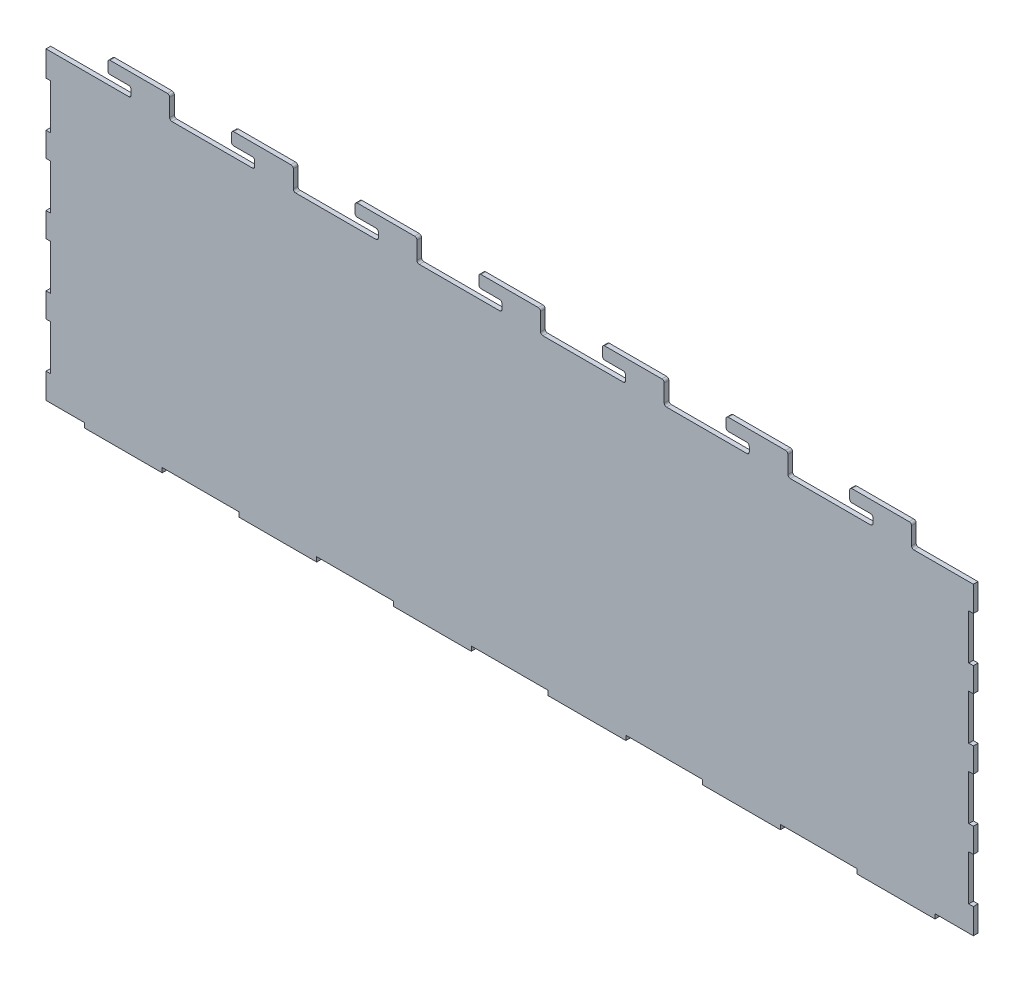
SolidWorks part; units mm, degrees
ref_plane "Alzado" through (0, 0, 0) normal (0, 0, 1) x (1, 0, 0)
ref_plane "Planta" through (0, 0, 0) normal (0, 1, 0) x (1, 0, 0)
ref_plane "Vista lateral" through (0, 0, 0) normal (1, 0, 0) x (0, 0, -1)
sketch "Croquis1" plane through (0, 0, 0) normal (0, 0, 1) x (1, 0, 0)
  line L1 (-300, 100) -> (300, 100)
  line L2 (-300, 100) -> (-300, -100)
  line L3 (-300, -100) -> (300, -100)
  line L4 (300, 100) -> (300, -100)
  line L5 (-300, 100) -> (300, -100) construction
  line L6 (-300, -100) -> (300, 100) construction
  point P0 (0, 0)
  dimension "D1" = 600
  dimension "D2" = 200
extrude "Saliente-Extruir1" add sketch "Croquis1" along normal blind 3
sketch "Croquis2" plane through (0, 0, 0) normal (0, 0, -1) x (-1, 0, 0)
  line L4 (-300, 100) -> (-300, -100)
  line L5 (-300, -100) -> (300, -100)
  line L6 (300, -100) -> (300, 100)
  line L7 (300, 100) -> (-300, 100)
  line L9 (-300, -100) -> (300, -100)
  line L11 (300, 100) -> (-300, 100)
  line L68 (224.85, -100) -> (275.15, -100)
  line L69 (275.15, -100) -> (275.15, -97)
  line L70 (275.15, -97) -> (300, -97)
  line L71 (300, -97) -> (300, -81)
  line L72 (300, -81) -> (297, -81)
  line L73 (297, -81) -> (297, -51)
  line L74 (297, -51) -> (300, -51)
  line L75 (300, -51) -> (300, -36)
  line L76 (300, -36) -> (297, -36)
  line L77 (297, -36) -> (297, -6)
  line L78 (297, -6) -> (300, -6)
  line L79 (300, -6) -> (300, 9)
  line L80 (300, 9) -> (297, 9)
  line L81 (297, 9) -> (297, 39)
  line L82 (297, 39) -> (300, 39)
  line L83 (300, 39) -> (300, 54)
  line L84 (300, 54) -> (297, 54)
  line L85 (297, 54) -> (297, 84)
  line L86 (297, 84) -> (300, 84)
  line L87 (300, 84) -> (300, 100)
  line L88 (300, 100) -> (-300, 100)
  line L89 (-300, 100) -> (-300, 84)
  line L90 (-300, 84) -> (-297, 84)
  line L91 (-297, 84) -> (-297, 54)
  line L92 (-297, 54) -> (-300, 54)
  line L93 (-300, 54) -> (-300, 39)
  line L94 (-300, 39) -> (-297, 39)
  line L95 (-297, 39) -> (-297, 9)
  line L96 (-297, 9) -> (-300, 9)
  line L97 (-300, 9) -> (-300, -6)
  line L98 (-300, -6) -> (-297, -6)
  line L99 (-297, -6) -> (-297, -36)
  line L100 (-297, -36) -> (-300, -36)
  line L101 (-300, -36) -> (-300, -51)
  line L102 (-300, -51) -> (-297, -51)
  line L103 (-297, -51) -> (-297, -81)
  line L104 (-297, -81) -> (-300, -81)
  line L105 (-300, -81) -> (-300, -97)
  line L106 (-300, -97) -> (-275.15, -97)
  line L107 (-275.15, -97) -> (-275.15, -100)
  line L108 (-275.15, -100) -> (-224.85, -100)
  line L109 (-224.85, -100) -> (-224.85, -97)
  line L110 (-224.85, -97) -> (-175.15, -97)
  line L111 (-175.15, -97) -> (-175.15, -100)
  line L112 (-175.15, -100) -> (-124.85, -100)
  line L113 (-124.85, -100) -> (-124.85, -97)
  line L114 (-124.85, -97) -> (-75.15, -97)
  line L115 (-75.15, -97) -> (-75.15, -100)
  line L116 (-75.15, -100) -> (-24.85, -100)
  line L117 (-24.85, -100) -> (-24.85, -97)
  line L118 (-24.85, -97) -> (24.85, -97)
  line L119 (24.85, -97) -> (24.85, -100)
  line L120 (24.85, -100) -> (75.15, -100)
  line L121 (75.15, -100) -> (75.15, -97)
  line L122 (75.15, -97) -> (124.85, -97)
  line L123 (124.85, -97) -> (124.85, -100)
  line L124 (124.85, -100) -> (175.15, -100)
  line L125 (175.15, -100) -> (175.15, -97)
  line L126 (175.15, -97) -> (224.85, -97)
  line L127 (224.85, -97) -> (224.85, -100)
  line L128 (224.85, -100) -> (275.15, -100)
  line L129 (275.15, -100) -> (275.15, -97)
  line L130 (275.15, -97) -> (300, -97)
  line L148 (300, 100) -> (-300, 100)
  line L166 (-300, -97) -> (-275.15, -97)
  line L167 (-275.15, -97) -> (-275.15, -100)
  line L168 (-275.15, -100) -> (-224.85, -100)
  line L169 (-224.85, -100) -> (-224.85, -97)
  line L170 (-224.85, -97) -> (-175.15, -97)
  line L171 (-175.15, -97) -> (-175.15, -100)
  line L172 (-175.15, -100) -> (-124.85, -100)
  line L173 (-124.85, -100) -> (-124.85, -97)
  line L174 (-124.85, -97) -> (-75.15, -97)
  line L175 (-75.15, -97) -> (-75.15, -100)
  line L176 (-75.15, -100) -> (-24.85, -100)
  line L177 (-24.85, -100) -> (-24.85, -97)
  line L178 (-24.85, -97) -> (24.85, -97)
  line L179 (24.85, -97) -> (24.85, -100)
  line L180 (24.85, -100) -> (75.15, -100)
  line L181 (75.15, -100) -> (75.15, -97)
  line L182 (75.15, -97) -> (124.85, -97)
  line L183 (124.85, -97) -> (124.85, -100)
  line L184 (124.85, -100) -> (175.15, -100)
  line L185 (175.15, -100) -> (175.15, -97)
  line L186 (175.15, -97) -> (224.85, -97)
  line L187 (224.85, -97) -> (224.85, -100)
  line L548 (-300, -97) -> (-300, 100)
  line L549 (300, -100) -> (300, 100)
  line L731 (-297, -51.4) -> (-300, -51.4)
  line L732 (-297, -51.4) -> (-297, -80.6)
  line L733 (-297, -80.6) -> (-300, -80.6)
  line L734 (-300, -51.4) -> (-300, -80.6)
  line L1814 (-297, -6.4) -> (-297, -35.6)
  line L1815 (-297, -6.4) -> (-300, -6.4)
  line L1816 (-300, -6.4) -> (-300, -35.6)
  line L1817 (-297, -35.6) -> (-300, -35.6)
  line L1818 (-297, 38.6) -> (-297, 9.4)
  line L1819 (-297, 38.6) -> (-300, 38.6)
  line L1820 (-300, 38.6) -> (-300, 9.4)
  line L1821 (-297, 9.4) -> (-300, 9.4)
  line L1822 (-297, 83.6) -> (-297, 54.4)
  line L1823 (-297, 83.6) -> (-300, 83.6)
  line L1824 (-300, 83.6) -> (-300, 54.4)
  line L1825 (-297, 54.4) -> (-300, 54.4)
  line L1826 (0, 0) -> (0, 54.4) construction
  line L1827 (297, -80.6) -> (300, -80.6)
  line L1828 (300, -51.4) -> (300, -80.6)
  line L1829 (297, -51.4) -> (300, -51.4)
  line L1830 (297, -51.4) -> (297, -80.6)
  line L1831 (297, -6.4) -> (300, -6.4)
  line L1832 (300, -6.4) -> (300, -35.6)
  line L1833 (297, -35.6) -> (300, -35.6)
  line L1834 (297, -6.4) -> (297, -35.6)
  line L1835 (297, 38.6) -> (300, 38.6)
  line L1836 (300, 38.6) -> (300, 9.4)
  line L1837 (297, 9.4) -> (300, 9.4)
  line L1838 (297, 38.6) -> (297, 9.4)
  line L1839 (297, 83.6) -> (300, 83.6)
  line L1840 (300, 83.6) -> (300, 54.4)
  line L1841 (297, 54.4) -> (300, 54.4)
  line L1842 (297, 83.6) -> (297, 54.4)
  dimension "D3" = 0
  dimension "D4" = 29.2
  dimension "D5" = 3
  dimension "D6" = 19.4
  dimension "D8" = 45
  dimension "D1" = 0
  dimension "D2" = 0
  dimension "D7" = 4
extrude "Cortar-Extruir1" cut sketch "Croquis2" against normal through all
sketch "Croquis3" plane through (0, 0, 0) normal (0, 0, -1) x (-1, 0, 0)
  line L0 (-235, 100) -> (-235, 104.8)
  line L1 (-300, 100) -> (300, 100) construction
  line L2 (-233.5, 106.3) -> (-221.5, 106.3)
  line L3 (-220, 107.8) -> (-220, 112.8)
  line L4 (-221.5, 114.3) -> (-258.5, 114.3)
  line L5 (-260, 112.8) -> (-260, 100)
  line L6 (-260, 100) -> (-235, 100)
  line L7 (-180, 100) -> (-155, 100)
  line L8 (-155, 100) -> (-155, 104.8)
  line L9 (-153.5, 106.3) -> (-141.5, 106.3)
  line L10 (-140, 107.8) -> (-140, 112.8)
  line L11 (-141.5, 114.3) -> (-178.5, 114.3)
  line L12 (-180, 112.8) -> (-180, 100)
  line L13 (-100, 100) -> (-75, 100)
  line L14 (-75, 100) -> (-75, 104.8)
  line L15 (-73.5, 106.3) -> (-61.5, 106.3)
  line L16 (-60, 107.8) -> (-60, 112.8)
  line L17 (-61.5, 114.3) -> (-98.5, 114.3)
  line L18 (-100, 112.8) -> (-100, 100)
  line L19 (-20, 100) -> (5, 100)
  line L20 (5, 100) -> (5, 104.8)
  line L21 (6.5, 106.3) -> (18.5, 106.3)
  line L22 (20, 107.8) -> (20, 112.8)
  line L23 (18.5, 114.3) -> (-18.5, 114.3)
  line L24 (-20, 112.8) -> (-20, 100)
  line L25 (60, 100) -> (85, 100)
  line L26 (85, 100) -> (85, 104.8)
  line L27 (86.5, 106.3) -> (98.5, 106.3)
  line L28 (100, 107.8) -> (100, 112.8)
  line L29 (98.5, 114.3) -> (61.5, 114.3)
  line L30 (60, 112.8) -> (60, 100)
  line L31 (140, 100) -> (165, 100)
  line L32 (165, 100) -> (165, 104.8)
  line L33 (166.5, 106.3) -> (178.5, 106.3)
  line L34 (180, 107.8) -> (180, 112.8)
  line L35 (178.5, 114.3) -> (141.5, 114.3)
  line L36 (140, 112.8) -> (140, 100)
  line L37 (220, 100) -> (245, 100)
  line L38 (245, 100) -> (245, 104.8)
  line L39 (246.5, 106.3) -> (258.5, 106.3)
  line L40 (260, 107.8) -> (260, 112.8)
  line L41 (258.5, 114.3) -> (221.5, 114.3)
  line L42 (220, 112.8) -> (220, 100)
  arc A0 (-220, 112.8) -> (-221.5, 114.3) centre (-221.5, 112.8) ccw
  arc A1 (-221.5, 106.3) -> (-220, 107.8) centre (-221.5, 107.8) ccw
  arc A2 (-235, 104.8) -> (-233.5, 106.3) centre (-233.5, 104.8) cw
  arc A3 (-258.5, 114.3) -> (-260, 112.8) centre (-258.5, 112.8) ccw
  arc A4 (260, 112.8) -> (258.5, 114.3) centre (258.5, 112.8) ccw
  arc A5 (258.5, 106.3) -> (260, 107.8) centre (258.5, 107.8) ccw
  arc A6 (245, 104.8) -> (246.5, 106.3) centre (246.5, 104.8) cw
  arc A7 (221.5, 114.3) -> (220, 112.8) centre (221.5, 112.8) ccw
  arc A8 (180, 112.8) -> (178.5, 114.3) centre (178.5, 112.8) ccw
  arc A9 (178.5, 106.3) -> (180, 107.8) centre (178.5, 107.8) ccw
  arc A10 (165, 104.8) -> (166.5, 106.3) centre (166.5, 104.8) cw
  arc A11 (141.5, 114.3) -> (140, 112.8) centre (141.5, 112.8) ccw
  arc A12 (100, 112.8) -> (98.5, 114.3) centre (98.5, 112.8) ccw
  arc A13 (98.5, 106.3) -> (100, 107.8) centre (98.5, 107.8) ccw
  arc A14 (85, 104.8) -> (86.5, 106.3) centre (86.5, 104.8) cw
  arc A15 (61.5, 114.3) -> (60, 112.8) centre (61.5, 112.8) ccw
  arc A16 (20, 112.8) -> (18.5, 114.3) centre (18.5, 112.8) ccw
  arc A17 (18.5, 106.3) -> (20, 107.8) centre (18.5, 107.8) ccw
  arc A18 (5, 104.8) -> (6.5, 106.3) centre (6.5, 104.8) cw
  arc A19 (-18.5, 114.3) -> (-20, 112.8) centre (-18.5, 112.8) ccw
  arc A20 (-60, 112.8) -> (-61.5, 114.3) centre (-61.5, 112.8) ccw
  arc A21 (-61.5, 106.3) -> (-60, 107.8) centre (-61.5, 107.8) ccw
  arc A22 (-75, 104.8) -> (-73.5, 106.3) centre (-73.5, 104.8) cw
  arc A23 (-98.5, 114.3) -> (-100, 112.8) centre (-98.5, 112.8) ccw
  arc A24 (-155, 104.8) -> (-153.5, 106.3) centre (-153.5, 104.8) cw
  arc A25 (-141.5, 106.3) -> (-140, 107.8) centre (-141.5, 107.8) ccw
  arc A26 (-140, 112.8) -> (-141.5, 114.3) centre (-141.5, 112.8) ccw
  arc A27 (-178.5, 114.3) -> (-180, 112.8) centre (-178.5, 112.8) ccw
  point P47 (-220, 114.3)
  point P50 (-220, 106.3)
  point P53 (-235, 106.3)
  point P56 (-260, 114.3)
  point P105 (-180, 114.3)
  dimension "D8" = 1.5
  dimension "D9" = 1.5
  dimension "D1" = 25
  dimension "D2" = 40
  dimension "D3" = 6.3
  dimension "D4" = 8
  dimension "D5" = 40
  dimension "D7" = 80
  dimension "D6" = 7
extrude "Saliente-Extruir2" add sketch "Croquis3" against normal blind 3
fillet "Redondeo1" radius 1.5 14 edges at (-220, 100, 1.5) (-140, 100, 1.5) (-60, 100, 1.5) (20, 100, 1.5) (100, 100, 1.5) (180, 100, 1.5) (-245, 100, 1.5) (-165, 100, 1.5) (-85, 100, 1.5) (-5, 100, 1.5) (75, 100, 1.5) (155, 100, 1.5) (235, 100, 1.5) (260, 100, 1.5)
